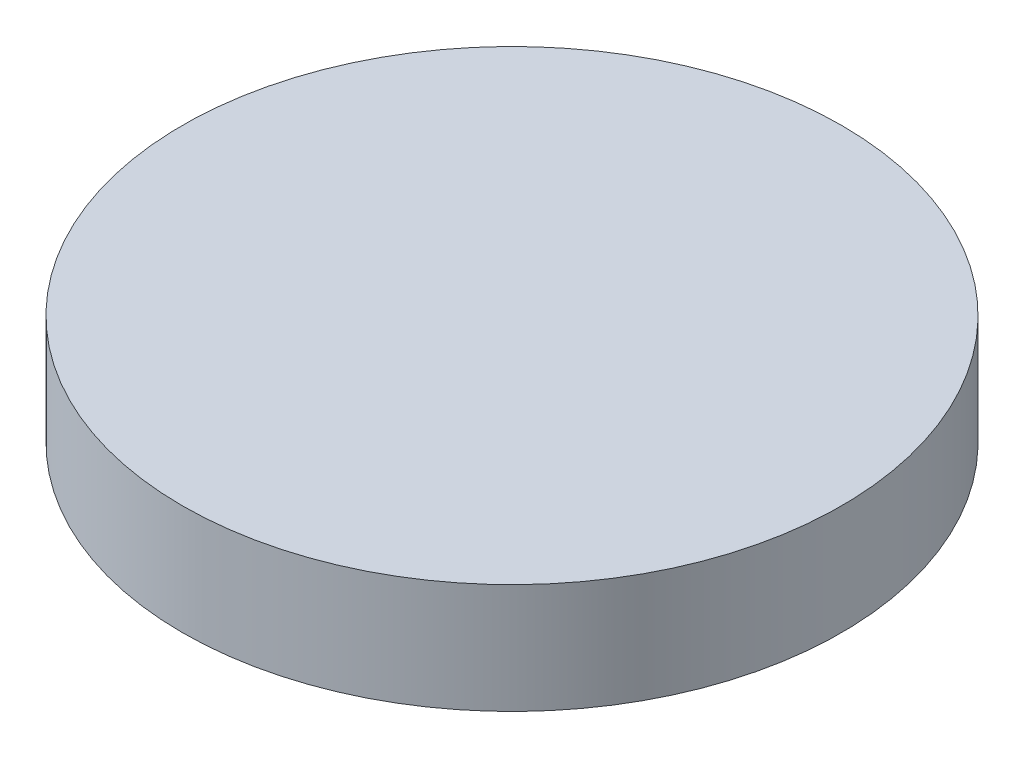
SolidWorks part; units mm, degrees
ref_plane "Front Plane" through (0, 0, 0) normal (0, 0, 1) x (1, 0, 0)
ref_plane "Top Plane" through (0, 0, 0) normal (0, 1, 0) x (1, 0, 0)
ref_plane "Right Plane" through (0, 0, 0) normal (1, 0, 0) x (0, 0, -1)
sketch "Sketch1" plane through (0, 0, 0) normal (0, 1, 0) x (1, 0, 0)
  circle A0 centre (0, 0) radius 30
  dimension "D1" = 60
extrude "Boss-Extrude1" add sketch "Sketch1" along normal mid plane 10
sketch "Sketch2" plane through (0, 0, 0) normal (0, 1, 0) x (1, 0, 0)
  line L1 (-12.5, -12.5) -> (12.5, -12.5) construction
  line L2 (-12.5, -12.5) -> (-12.5, 12.5) construction
  line L3 (-12.5, 12.5) -> (12.5, 12.5) construction
  line L4 (12.5, -12.5) -> (12.5, 12.5) construction
  line L5 (-12.5, -12.5) -> (12.5, 12.5) construction
  line L6 (-12.5, 12.5) -> (12.5, -12.5) construction
  circle A0 centre (-12.5, 12.5) radius 2.65
  circle A1 centre (12.5, 12.5) radius 2.65
  circle A2 centre (12.5, -12.5) radius 2.65
  circle A3 centre (-12.5, -12.5) radius 2.65
  point P0 (0, 0)
  dimension "D2" = 5.3
  dimension "D1" = 25
extrude "Cut-Extrude1" cut sketch "Sketch2" against normal mid plane 5.2
